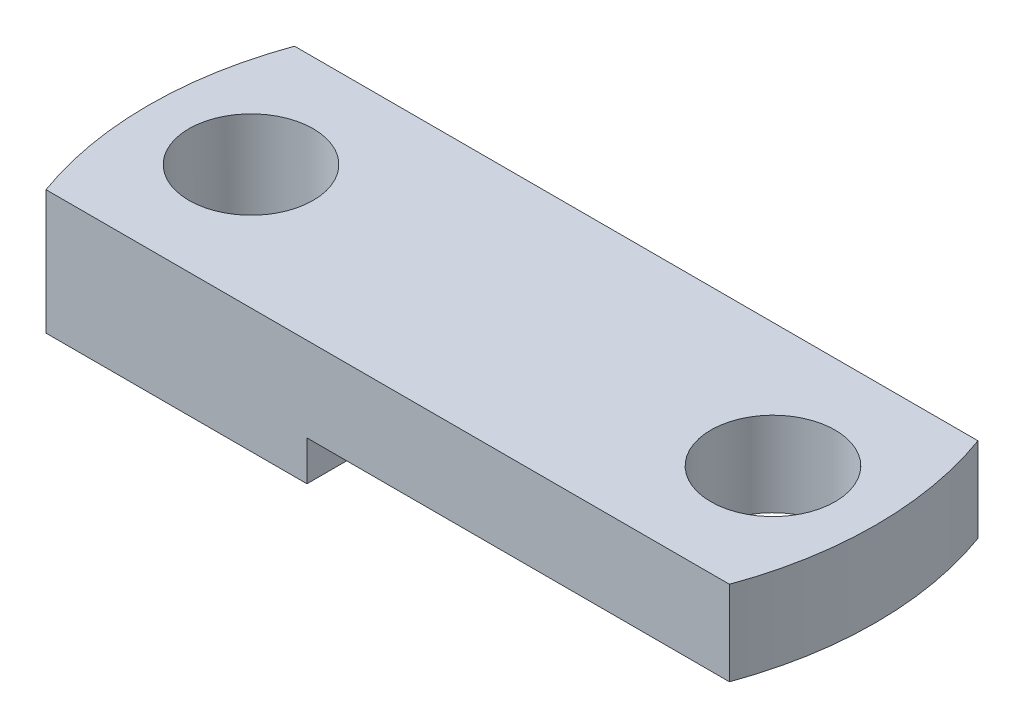
SolidWorks part; units mm, degrees
ref_plane "Front Plane" through (0, 0, 0) normal (0, 0, 1) x (1, 0, 0)
ref_plane "Top Plane" through (0, 0, 0) normal (0, 1, 0) x (1, 0, 0)
ref_plane "Right Plane" through (0, 0, 0) normal (1, 0, 0) x (0, 0, -1)
sketch "Sketch3" plane through (0, 0, 0) normal (0, 1, 0) x (1, 0, 0)
  line L1 (-17.4625, 6.35) -> (17.4625, 6.35)
  line L3 (-17.4625, -6.35) -> (17.4625, -6.35)
  line L5 (-17.4625, 6.35) -> (17.4625, -6.35) construction
  line L6 (-17.4625, -6.35) -> (17.4625, 6.35) construction
  arc A0 (-17.4625, 6.35) -> (-17.4625, -6.35) centre (0, 0) ccw
  arc A1 (17.4625, -6.35) -> (17.4625, 6.35) centre (0, 0) ccw
  point P0 (0, 0)
  dimension "D1" = 12.7
  dimension "D2" = 34.925
extrude "Boss-Extrude2" add sketch "Sketch3" along normal blind 6.35
sketch "Sketch4" plane through (0, 6.35, 0) normal (0, 1, 0) x (1, 0, 0)
  line L0 (-18.5812, 0) -> (18.5812, 0) construction
  line L1 (0, 6.35) -> (0, -6.35) construction
  line L2 (17.4625, 6.35) -> (-17.4625, 6.35) construction
  line L3 (-17.4625, -6.35) -> (17.4625, -6.35) construction
  arc A0 (-17.4625, 6.35) -> (-17.4625, -6.35) centre (0, 0) ccw construction
  arc A1 (17.4625, -6.35) -> (17.4625, 6.35) centre (0, 0) ccw construction
  circle A6 centre (13.335, 0) radius 3.175
  circle A7 centre (-13.335, 0) radius 3.175
  dimension "D1" = 26.67
  dimension "D5" = 6.35
extrude "Cut-Extrude1" cut sketch "Sketch4" against normal blind 12.7
sketch "Sketch5" plane through (0, 0, 0) normal (0, -1, 0) x (1, 0, 0)
  line L0 (17.4625, -6.35) -> (-17.4625, -6.35) construction
  line L1 (17.4625, 6.35) -> (-4.1275, 6.35)
  line L3 (17.4625, -6.35) -> (-4.1275, -6.35)
  line L4 (-4.1275, 6.35) -> (-4.1275, -6.35)
  arc A0 (17.4625, 6.35) -> (17.4625, -6.35) centre (0, 0) cw
  arc A1 (17.4625, -6.35) -> (17.4625, 6.35) centre (0, 0) ccw construction
  dimension "D1" = 21.59
extrude "Cut-Extrude2" cut sketch "Sketch5" against normal blind 2.032
